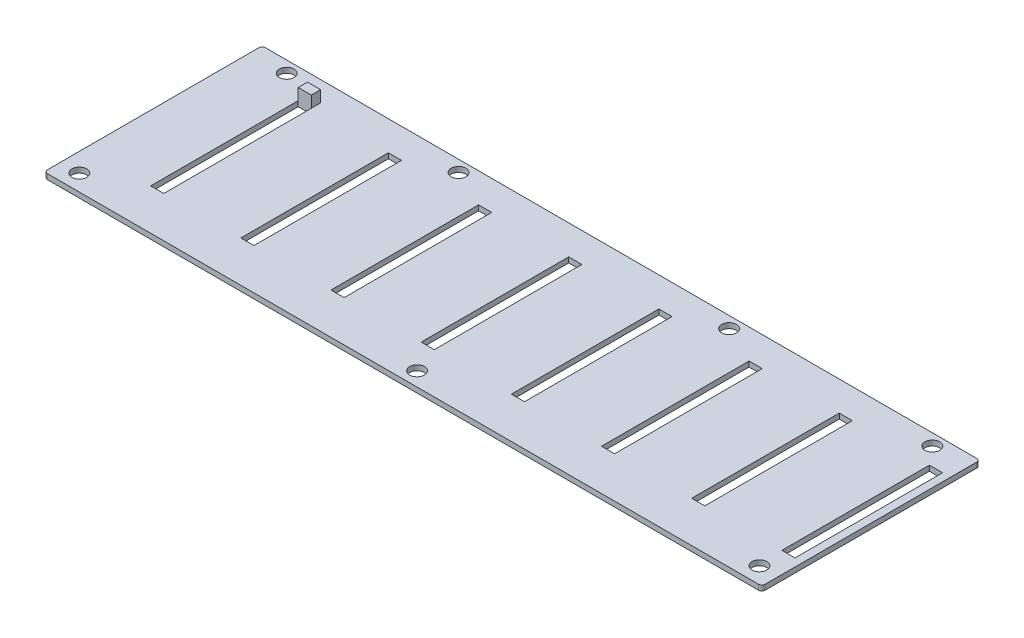
SolidWorks part; units mm, degrees
ref_plane "Front Plane" through (0, 0, 0) normal (0, 0, 1) x (1, 0, 0)
ref_plane "Top Plane" through (0, 0, 0) normal (0, 1, 0) x (1, 0, 0)
ref_plane "Right Plane" through (0, 0, 0) normal (1, 0, 0) x (0, 0, -1)
sketch "Sketch1" plane through (0, 0, 0) normal (0, 1, 0) x (1, 0, 0)
  line L0 (-343.6338, -10.1642) -> (262.3662, -10.1642) construction
  line L1 (0, 0) -> (218.9, 0)
  line L2 (0, 0) -> (0, 66.5)
  line L3 (0, 66.5) -> (218.9, 66.5)
  line L4 (218.9, 0) -> (218.9, 66.5)
  line L6 (20, 57.5) -> (24, 57.5)
  line L7 (20, 57.5) -> (20, 12.5)
  line L8 (20, 12.5) -> (24, 12.5)
  line L9 (24, 57.5) -> (24, 12.5)
  line L10 (47.5, 57.5) -> (51.5, 57.5)
  line L11 (47.5, 57.5) -> (47.5, 12.5)
  line L12 (47.5, 12.5) -> (51.5, 12.5)
  line L13 (51.5, 57.5) -> (51.5, 12.5)
  line L14 (75, 57.5) -> (79, 57.5)
  line L15 (75, 57.5) -> (75, 12.5)
  line L16 (75, 12.5) -> (79, 12.5)
  line L17 (79, 57.5) -> (79, 12.5)
  line L18 (102.5, 57.5) -> (106.5, 57.5)
  line L19 (102.5, 57.5) -> (102.5, 12.5)
  line L20 (102.5, 12.5) -> (106.5, 12.5)
  line L21 (106.5, 57.5) -> (106.5, 12.5)
  line L22 (130, 57.5) -> (134, 57.5)
  line L23 (130, 57.5) -> (130, 12.5)
  line L24 (130, 12.5) -> (134, 12.5)
  line L25 (134, 57.5) -> (134, 12.5)
  line L26 (157.5, 57.5) -> (161.5, 57.5)
  line L27 (157.5, 57.5) -> (157.5, 12.5)
  line L28 (157.5, 12.5) -> (161.5, 12.5)
  line L29 (161.5, 57.5) -> (161.5, 12.5)
  line L30 (185, 57.5) -> (189, 57.5)
  line L31 (185, 57.5) -> (185, 12.5)
  line L32 (185, 12.5) -> (189, 12.5)
  line L33 (189, 57.5) -> (189, 12.5)
  line L34 (212.5, 57.5) -> (216.5, 57.5)
  line L35 (212.5, 57.5) -> (212.5, 12.5)
  line L36 (212.5, 12.5) -> (216.5, 12.5)
  line L37 (216.5, 57.5) -> (216.5, 12.5)
  circle A0 centre (11, 63) radius 2.25
  circle A1 centre (63.4, 63) radius 2.25
  circle A2 centre (145.9, 63) radius 2.25
  circle A3 centre (207.9, 63) radius 2.25
  circle A4 centre (5.75, 5) radius 2.25
  circle A5 centre (109.45, 4.3) radius 2.25
  circle A6 centre (213.15, 5) radius 2.25
  dimension "D3" = 3.5
  dimension "D5" = 3.5
  dimension "D7" = 3.5
  dimension "D9" = 3.5
  dimension "D11" = 5
  dimension "D13" = 4.3
  dimension "D15" = 5
  dimension "D1" = 218.9
  dimension "D2" = 66.5
  dimension "D4" = 11
  dimension "D6" = 52.4
  dimension "D8" = 82.5
  dimension "D10" = 62
  dimension "D12" = 5.75
  dimension "D14" = 103.7
  dimension "D16" = 103.7
  dimension "D17" = 4
  dimension "D18" = 45
  dimension "D19" = 20
  dimension "D20" = 9
  dimension "D21" = 27.5
  dimension "D22" = 4
  dimension "D23" = 45
  dimension "D24" = 9
  dimension "D25" = 4
  dimension "D26" = 45
  dimension "D27" = 9
  dimension "D28" = 27.5
  dimension "D29" = 27.5
  dimension "D30" = 4
  dimension "D31" = 45
  dimension "D32" = 9
  dimension "D33" = 27.5
  dimension "D34" = 45
  dimension "D35" = 4
  dimension "D36" = 9
  dimension "D37" = 27.5
  dimension "D38" = 4
  dimension "D39" = 45
  dimension "D40" = 9
  dimension "D41" = 27.5
  dimension "D42" = 4
  dimension "D43" = 45
  dimension "D44" = 9
  dimension "D45" = 45
  dimension "D46" = 9
  dimension "D47" = 27.5
  dimension "D48" = 4
extrude "Boss-Extrude1" add sketch "Sketch1" along normal blind 1.6
fillet "Fillet1" radius 1 4 edges at (218.9, 0.8, -66.5) (218.9, 0.8, 0) (0, 0.8, 0) (0, 0.8, -66.5)
ref_plane "Plane1" through (20, 1.6, -12.5) normal (0, 0, 1) x (1, 0, 0)
sketch "Sketch3" plane through (0, 0, 0) normal (0, 1, 0) x (1, 0, 0)
  line L1 (20, 57.5) -> (24, 57.5)
  line L2 (20, 57.5) -> (20, 60.3316)
  line L3 (20, 60.3316) -> (24, 60.3316)
  line L4 (24, 57.5) -> (24, 60.3316)
  dimension "D1" = 4
extrude "Boss-Extrude2" add sketch "Sketch3" along normal blind 5.1
